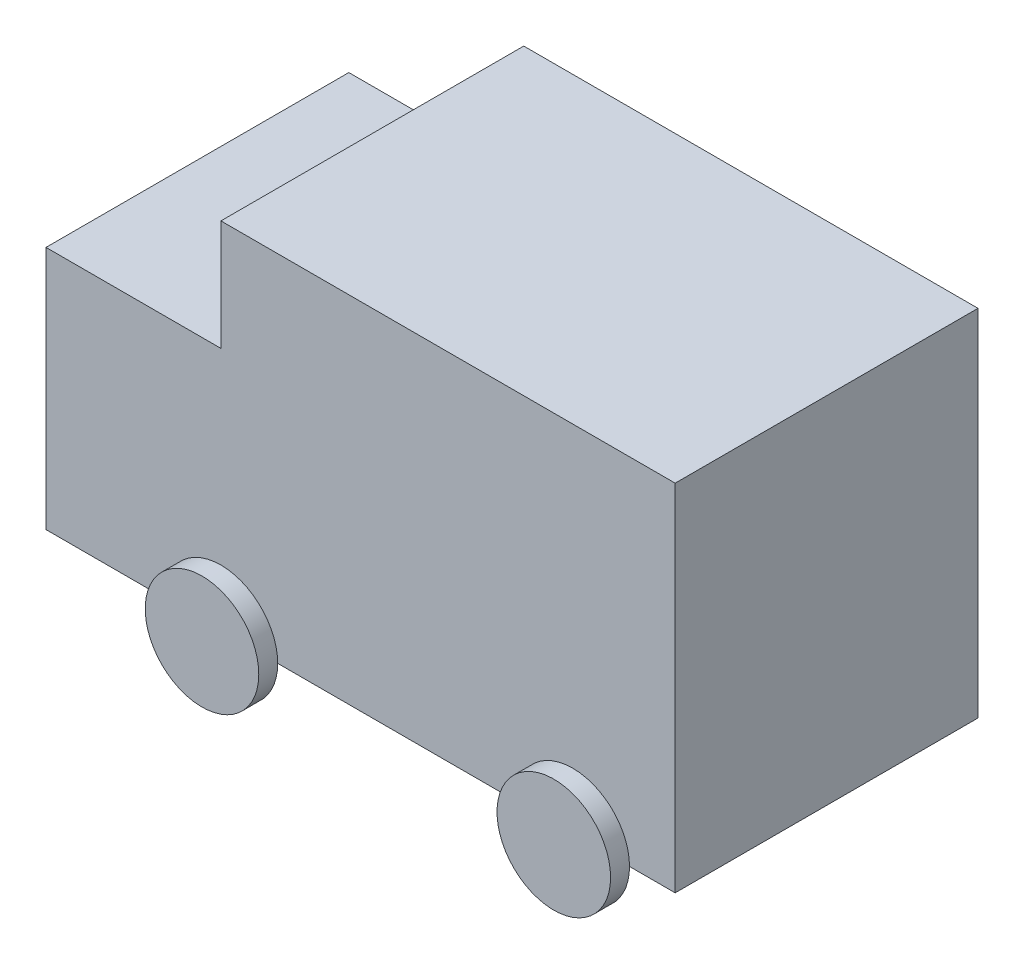
SolidWorks part; units mm, degrees
ref_plane "Front Plane" through (0, 0, 0) normal (0, 0, 1) x (1, 0, 0)
ref_plane "Top Plane" through (0, 0, 0) normal (0, 1, 0) x (1, 0, 0)
ref_plane "Right Plane" through (0, 0, 0) normal (1, 0, 0) x (0, 0, -1)
sketch "Sketch1" plane through (0, 0, 0) normal (0, 1, 0) x (1, 0, 0)
  line L1 (0, -1219.2) -> (3657.6, -1219.2)
  line L2 (0, -1219.2) -> (0, 1219.2)
  line L3 (0, 1219.2) -> (3657.6, 1219.2)
  line L4 (3657.6, -1219.2) -> (3657.6, 1219.2)
  dimension "D1" = 3657.6
  dimension "D2" = 2438.4
extrude "Boss-Extrude1" add sketch "Sketch1" along normal blind 2857 contours L2 L1 L4 L3
sketch "Sketch2" plane through (0, 0, 0) normal (0, 1, 0) x (1, 0, 0)
  line L0 (0, -1219.2) -> (3657.6, -1219.2) construction
  line L1 (0, 1219.2) -> (-1408.4463, 1219.2)
  line L2 (0, 1219.2) -> (0, -1219.2)
  line L3 (0, -1219.2) -> (-1408.4463, -1219.2)
  line L4 (-1408.4463, 1219.2) -> (-1408.4463, -1219.2)
  point P5 (0, 0)
  point P8 (-1408.4463, -1219.2)
extrude "Boss-Extrude2" add sketch "Sketch2" along normal blind 1968
sketch "Sketch3" plane through (0, 0, 1219.2) normal (0, 0, 1) x (1, 0, 0)
  line L0 (0, 0) -> (2832.8015, 0) construction
  line L1 (-1408.4463, 0) -> (3657.6, 0) construction
  circle A0 centre (0, 0) radius 457.2
  circle A1 centre (2832.8015, 0) radius 457.2
  dimension "D1" = 914.4
extrude "Boss-Extrude3" add sketch "Sketch3" along normal blind 152.4
mirror "Mirror1" about plane through (0, 0, 0) normal (0, 0, 1) of "Boss-Extrude3"
